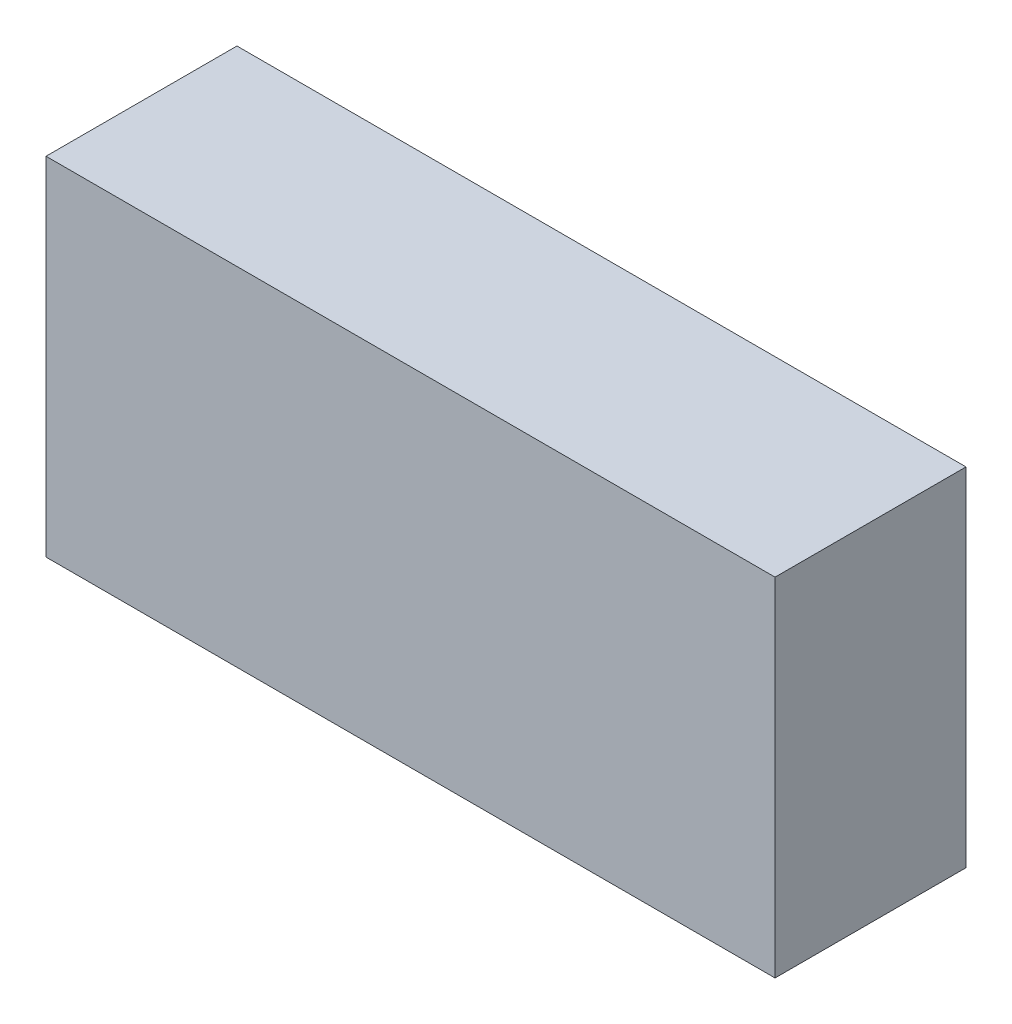
SolidWorks part; units mm, degrees
ref_plane "Plan de face" through (0, 0, 0) normal (0, 0, 1) x (1, 0, 0)
ref_plane "Plan de dessus" through (0, 0, 0) normal (0, 1, 0) x (1, 0, 0)
ref_plane "Plan de droite" through (0, 0, 0) normal (1, 0, 0) x (0, 0, -1)
sketch "Esquisse1" plane through (0, 0, 0) normal (0, 0, 1) x (1, 0, 0)
  line L1 (-93.044, 40.9114) -> (116.956, 40.9114)
  line L2 (-93.044, 40.9114) -> (-93.044, -59.0886)
  line L3 (-93.044, -59.0886) -> (116.956, -59.0886)
  line L4 (116.956, 40.9114) -> (116.956, -59.0886)
  dimension "D1" = 210
  dimension "D2" = 100
extrude "Boss.-Extru.1" add sketch "Esquisse1" along normal blind 55
